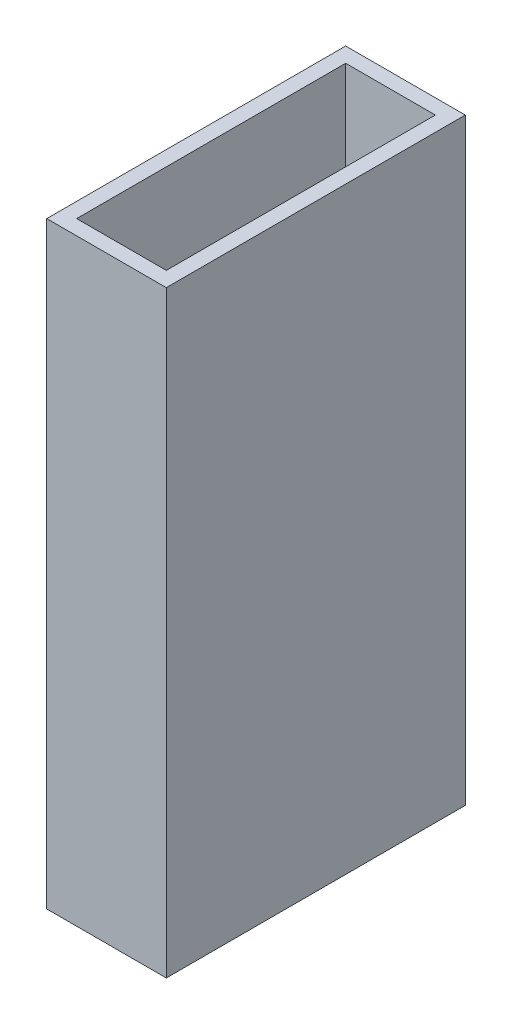
SolidWorks part; units mm, degrees
ref_plane "Front Plane" through (0, 0, 0) normal (0, 0, 1) x (1, 0, 0)
ref_plane "Top Plane" through (0, 0, 0) normal (0, 1, 0) x (1, 0, 0)
ref_plane "Right Plane" through (0, 0, 0) normal (1, 0, 0) x (0, 0, -1)
sketch "Sketch1" plane through (0, 0, 0) normal (0, 1, 0) x (1, 0, 0)
  line L0 (0, 69.5918) -> (0, -86.5306) construction
  line L1 (-20, 50) -> (20, 50)
  line L2 (-20, 50) -> (-20, -50)
  line L3 (-20, -50) -> (20, -50)
  line L4 (20, 50) -> (20, -50)
  line L5 (-104.4898, 0) -> (80.2041, 0) construction
  dimension "D1" = 100
  dimension "D2" = 40
extrude "Boss-Extrude1" add sketch "Sketch1" along normal blind 200
shell "Shell2" thickness 5
